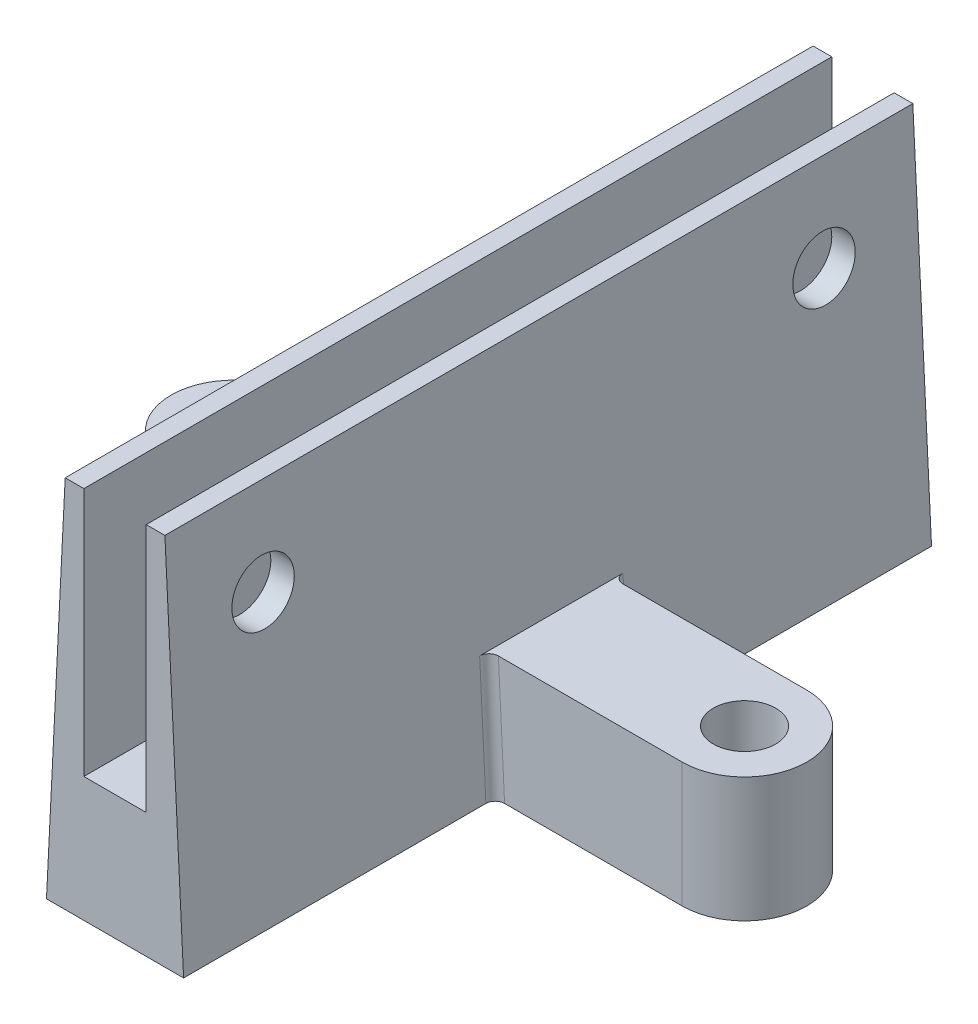
SolidWorks part; units mm, degrees
ref_plane "Front Plane" through (0, 0, 0) normal (0, 0, 1) x (1, 0, 0)
ref_plane "Top Plane" through (0, 0, 0) normal (0, 1, 0) x (1, 0, 0)
ref_plane "Right Plane" through (0, 0, 0) normal (1, 0, 0) x (0, 0, -1)
sketch "Sketch1" plane through (0, 0, 0) normal (0, 0, 1) x (1, 0, 0)
  line L0 (0, 0) -> (22, 0)
  line L1 (6, 20) -> (6, 60)
  line L2 (16, 20) -> (16, 60)
  line L3 (6, 20) -> (16, 20)
  line L4 (6, 60) -> (3, 60)
  line L5 (16, 60) -> (19, 60)
  line L6 (0, 0) -> (3, 60)
  line L7 (22, 0) -> (19, 60)
  dimension "D1" = 22
  dimension "D2" = 10
  dimension "D3" = 6
  dimension "D4" = 3
  dimension "D5" = 3
  dimension "D6" = 20
  dimension "D7" = 60
  dimension "D8" = 60
extrude "Boss-Extrude1" add sketch "Sketch1" along normal blind 120
ref_plane "Plane1" through (22, 0, 0) normal (1, 0, 0) x (0, 0, -1)
ref_plane "Plane2" through (0, 0, 0) normal (1, 0, 0) x (0, 0, -1)
sketch "Sketch10" plane through (0, 0, 0) normal (1, 0, 0) x (0, 0, -1)
  line L0 (-120, 0) -> (0, 0) construction
  line L1 (-70, 20) -> (-50, 20)
  line L2 (-70, 20) -> (-70, 0)
  line L3 (-70, 0) -> (-50, 0)
  line L4 (-50, 20) -> (-50, 0)
  line L5 (-60, 20) -> (-60, 0) construction
  dimension "D1" = 20
  dimension "D2" = 20
  dimension "D3" = 60
extrude "Boss-Extrude6" add sketch "Sketch10" against normal blind 30 and the other way blind 4 contours L2 L1 L4 L3
sketch "Sketch13" plane through (22, 0, 0) normal (1, 0, 0) x (0, 0, -1)
  line L0 (-120, 0) -> (0, 0) construction
  line L1 (-70, 0) -> (-50, 0)
  line L2 (-70, 0) -> (-70, 20)
  line L3 (-70, 20) -> (-50, 20)
  line L4 (-50, 0) -> (-50, 20)
  line L5 (-60, 20) -> (-60, 0) construction
  dimension "D1" = 20
  dimension "D2" = 20
  dimension "D3" = 60
extrude "Boss-Extrude8" add sketch "Sketch13" along normal blind 30 and the other way blind 5 contours L2 L1 L4 L3
sketch "Sketch14" plane through (0, 0, 0) normal (0, -1, 0) x (1, 0, 0)
  line L0 (-30, 70) -> (-30, 50) construction
  line L1 (0, 70) -> (-30, 70) construction
  line L2 (52, 70) -> (52, 50) construction
  line L3 (22, 50) -> (52, 50) construction
  line L4 (-30, 70) -> (-30, 50)
  line L5 (52, 70) -> (52, 50)
  arc A0 (-30, 70) -> (-30, 50) centre (-30, 60) ccw
  arc A1 (52, 70) -> (52, 50) centre (52, 60) cw
extrude "Boss-Extrude9" add sketch "Sketch14" against normal blind 20
sketch "Sketch15" plane through (0, 0, 0) normal (0, -1, 0) x (1, 0, 0)
  circle A0 centre (-30, 60) radius 5
  arc A1 (-30, 70) -> (-30, 50) centre (-30, 60) ccw construction
  circle A2 centre (52, 60) radius 5
  arc A3 (52, 50) -> (52, 70) centre (52, 60) ccw construction
  dimension "D1" = 10
  dimension "D2" = 10
extrude "Cut-Extrude5" cut sketch "Sketch15" against normal blind 20
fillet "Fillet2" radius 1.5 4 edges at (0.5, 10, 50) (0.5, 10, 70) (21.5, 10, 50) (21.5, 10, 70)
sketch "Sketch16" plane through (6, 0, 0) normal (1, 0, 0) x (0, 0, -1)
  line L0 (-120, 60) -> (0, 60) construction
  line L1 (-120, 0) -> (-120, 60) construction
  line L2 (0, 0) -> (0, 60) construction
  circle A0 centre (-105, 45) radius 5
  circle A1 centre (-15, 45) radius 5
  point P4 (0, 0)
  dimension "D1" = 10
  dimension "D2" = 10
  dimension "D3" = 15
  dimension "D4" = 15
  dimension "D5" = 15
  dimension "D6" = 15
extrude "Cut-Extrude6" cut sketch "Sketch16" against normal blind 20 and the other way blind 20
